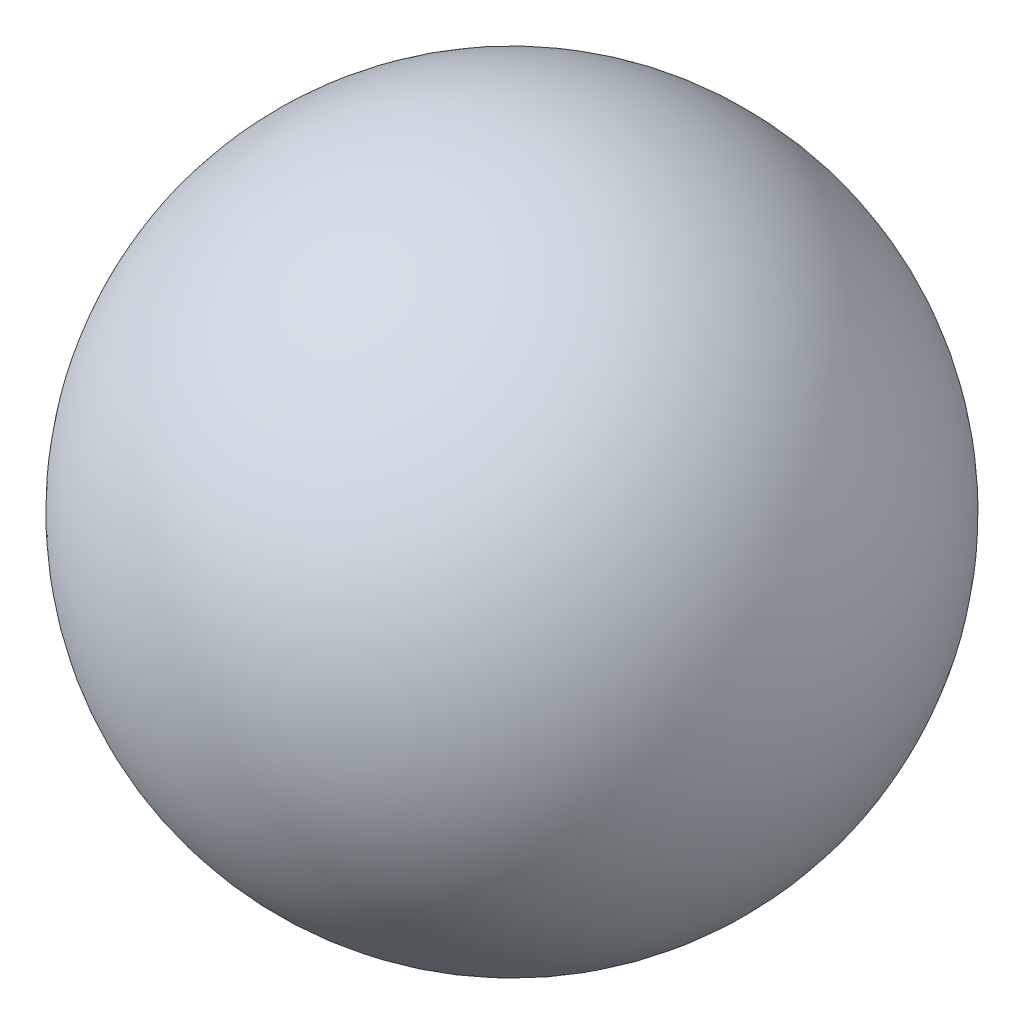
SolidWorks part; units mm, degrees
material "Rubber"
ref_plane "Front Plane" through (0, 0, 0) normal (0, 0, 1) x (1, 0, 0)
ref_plane "Top Plane" through (0, 0, 0) normal (0, 1, 0) x (1, 0, 0)
ref_plane "Right Plane" through (0, 0, 0) normal (1, 0, 0) x (0, 0, -1)
sketch "Sketch1" plane through (0, 0, 0) normal (0, 0, 1) x (1, 0, 0)
  line L2 (-75, 0) -> (75, 0)
  arc A2 (-75, 0) -> (75, 0) centre (0, 0) cw
  dimension "D1" = 75
revolve "Revolve4" add sketch "Sketch1" angle 360 about L2
